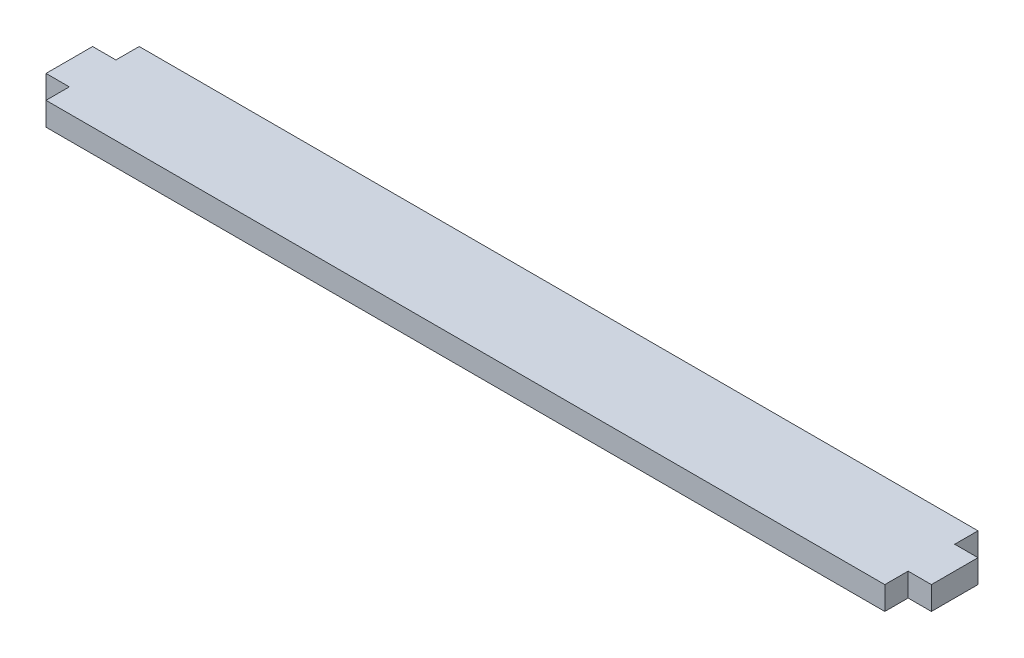
SolidWorks part; units mm, degrees
ref_plane "Front Plane" through (0, 0, 0) normal (0, 0, 1) x (1, 0, 0)
ref_plane "Top Plane" through (0, 0, 0) normal (0, 1, 0) x (1, 0, 0)
ref_plane "Right Plane" through (0, 0, 0) normal (1, 0, 0) x (0, 0, -1)
sketch "Sketch1" plane through (0, 0, 0) normal (0, 1, 0) x (1, 0, 0)
  line L0 (-57.15, 12.7) -> (-57.15, 0) construction
  line L1 (0, 0) -> (-114.3, 0)
  line L2 (0, 0) -> (0, 3.175)
  line L3 (0, 12.7) -> (-114.3, 12.7)
  line L4 (-114.3, 0) -> (-114.3, 3.175)
  line L5 (-114.3, 9.525) -> (-114.3, 12.7)
  line L6 (-114.3, 9.525) -> (-117.475, 9.525)
  line L7 (0, 3.175) -> (3.175, 3.175)
  line L8 (-114.3, 3.175) -> (-117.475, 3.175)
  line L9 (-117.475, 9.525) -> (-117.475, 3.175)
  line L10 (3.175, 9.525) -> (3.175, 3.175)
  line L11 (0, 9.525) -> (3.175, 9.525)
  line L12 (0, 9.525) -> (0, 12.7)
  dimension "D1" = 12.7
  dimension "D2" = 114.3
  dimension "D3" = 3.175
  dimension "D4" = 6.35
  dimension "D5" = 3.175
extrude "Boss-Extrude1" add sketch "Sketch1" along normal blind 3.175
